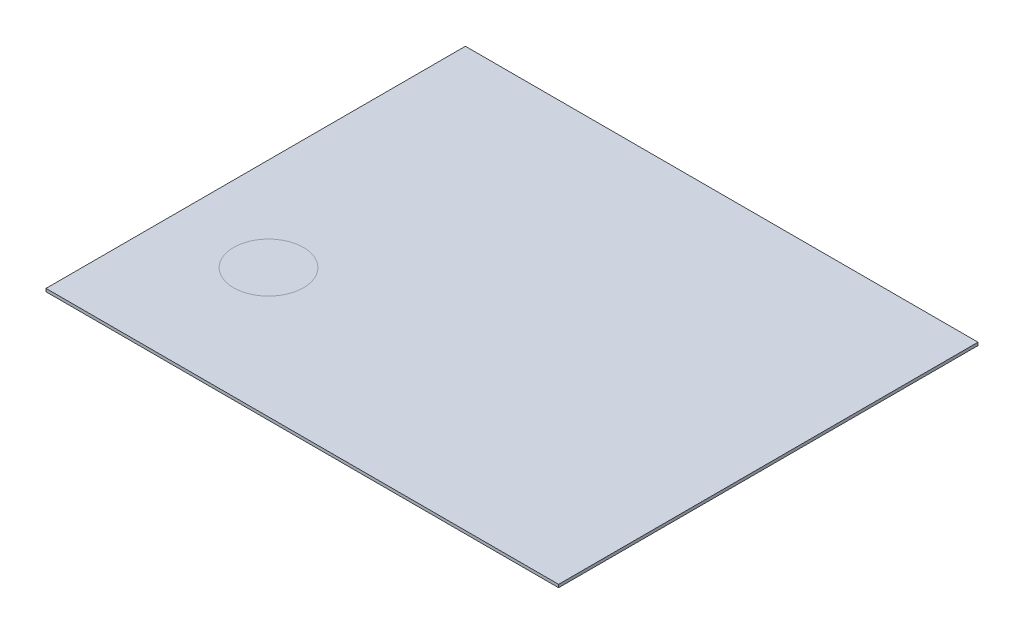
SolidWorks part; units mm, degrees
ref_plane "Front Plane" through (0, 0, 0) normal (0, 0, 1) x (1, 0, 0)
ref_plane "Top Plane" through (0, 0, 0) normal (0, 1, 0) x (1, 0, 0)
ref_plane "Right Plane" through (0, 0, 0) normal (1, 0, 0) x (0, 0, -1)
sketch "Sketch1" plane through (0, 0, 0) normal (0, 1, 0) x (1, 0, 0)
  line L1 (550, -450) -> (-550, -450)
  line L2 (550, -450) -> (550, 450)
  line L3 (550, 450) -> (-550, 450)
  line L4 (-550, -450) -> (-550, 450)
  line L5 (550, -450) -> (-550, 450) construction
  line L6 (550, 450) -> (-550, -450) construction
  point P0 (0, 0)
  dimension "D1" = 900
  dimension "D2" = 1100
extrude "Boss-Extrude1" add sketch "Sketch1" along normal blind 6.35
sketch "Sketch2" plane through (0, 6.35, 0) normal (0, 1, 0) x (1, 0, 0)
  circle A0 centre (-349.8545, -172.6) radius 75
  point P0 (-349.8545, -172.6)
  dimension "D1" = 150
split line "Split Line1"
